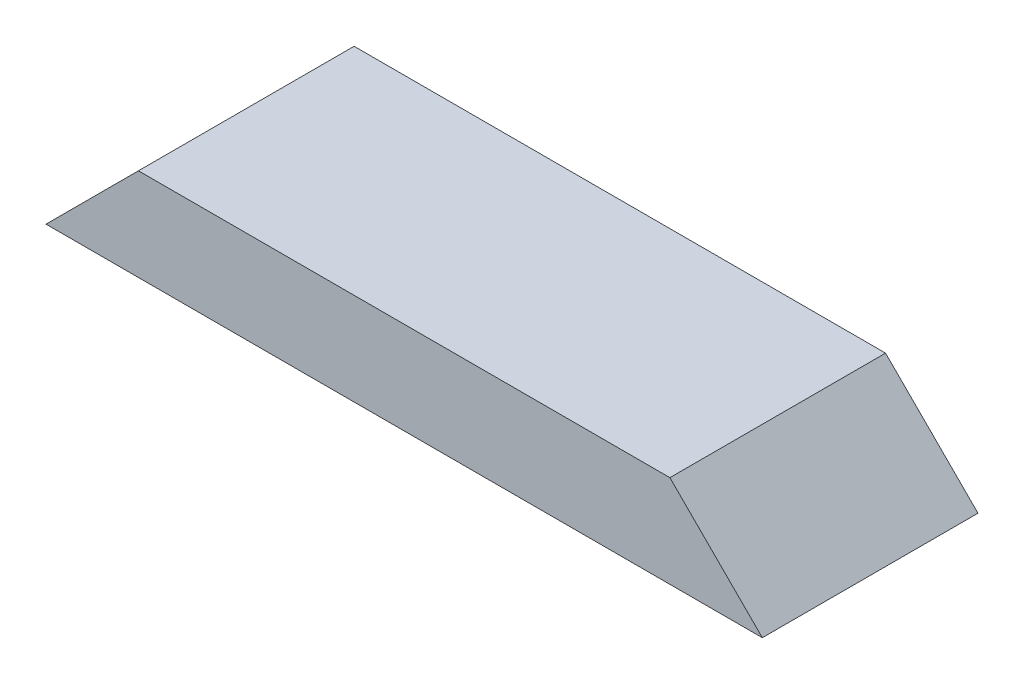
SolidWorks part; units mm, degrees
material "Pine"
ref_plane "Front Plane" through (0, 0, 0) normal (0, 0, 1) x (1, 0, 0)
ref_plane "Top Plane" through (0, 0, 0) normal (0, 1, 0) x (1, 0, 0)
ref_plane "Right Plane" through (0, 0, 0) normal (1, 0, 0) x (0, 0, -1)
sketch "Sketch1" plane through (0, 0, 0) normal (0, 1, 0) x (1, 0, 0)
  line L1 (0, 0) -> (295.275, 0)
  line L2 (0, 0) -> (0, 88.9)
  line L3 (0, 88.9) -> (295.275, 88.9)
  line L4 (295.275, 0) -> (295.275, 88.9)
  dimension "D1" = 88.9
  dimension "D2" = 295.275
extrude "Boss-Extrude1" add sketch "Sketch1" along normal blind 38.1
sketch "Sketch2" plane through (0, 0, 0) normal (0, 0, 1) x (1, 0, 0)
  line L0 (0, 0) -> (38.1, 38.1)
  line L1 (0, 38.1) -> (295.275, 38.1) construction
  line L2 (38.1, 38.1) -> (0, 38.1)
  line L3 (0, 38.1) -> (0, 0)
  line L5 (295.275, 0) -> (295.275, 38.1)
  line L9 (295.275, 38.1) -> (257.175, 38.1)
  line L10 (257.175, 38.1) -> (295.275, 0)
  dimension "D1" = 38.1
  dimension "D2" = 38.1
  dimension "D3" = 38.1
extrude "Cut-Extrude1" cut sketch "Sketch2" against normal through all
